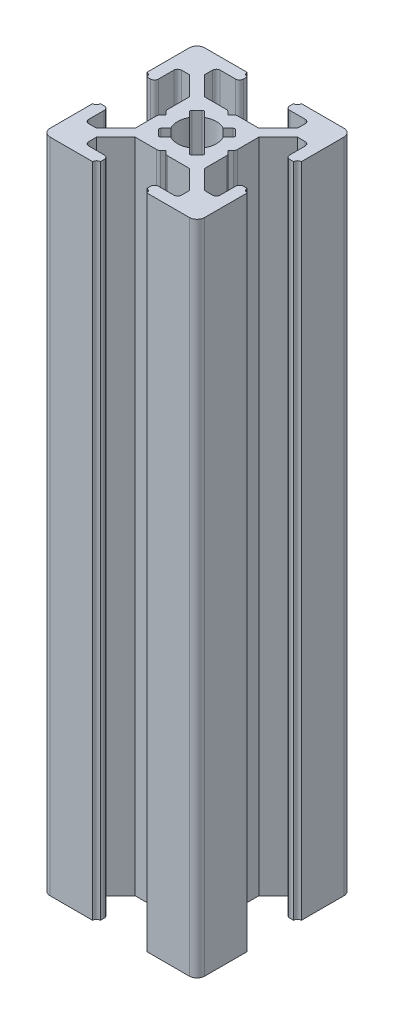
SolidWorks part; units mm, degrees
ref_plane "Front Plane" through (0, 0, 0) normal (0, 0, 1) x (1, 0, 0)
ref_plane "Top Plane" through (0, 0, 0) normal (0, 1, 0) x (1, 0, 0)
ref_plane "Right Plane" through (0, 0, 0) normal (1, 0, 0) x (0, 0, -1)
sketch "Sketch3" plane through (0, 0, 0) normal (0, 1, 0) x (1, 0, 0)
  line L0 (7, 20) -> (7, 18.5)
  line L1 (0, 0) -> (20, 0)
  line L2 (0, 0) -> (0, 20)
  line L3 (0, 20) -> (20, 20)
  line L4 (20, 0) -> (20, 20)
  line L5 (7, 18.5) -> (4, 18.5)
  line L6 (4, 18.5) -> (4, 17)
  line L7 (4, 17) -> (6.5, 14.5)
  line L8 (6.5, 14.5) -> (13.5, 14.5)
  line L9 (13.5, 14.5) -> (16, 17)
  line L10 (16, 17) -> (16, 18.5)
  line L11 (16, 18.5) -> (13, 18.5)
  line L12 (13, 18.5) -> (13, 20)
  line L13 (13, 20) -> (7, 20)
  line L14 (9.5, 14.5) -> (10, 14)
  line L15 (10, 14) -> (10.5, 14.5)
  line L16 (10.5, 14.5) -> (9.5, 14.5)
  line L17 (13, 19.5) -> (13, 20)
  line L18 (13.5, 20) -> (13, 20)
  line L19 (7, 19.5) -> (7, 20)
  line L20 (6.5, 20) -> (7, 20)
  line L21 (0, 13) -> (1.5, 13)
  line L22 (1.5, 13) -> (1.5, 16)
  line L23 (1.5, 16) -> (3, 16)
  line L24 (3, 16) -> (5.5, 13.5)
  line L25 (5.5, 13.5) -> (5.5, 6.5)
  line L26 (5.5, 6.5) -> (3, 4)
  line L27 (3, 4) -> (1.5, 4)
  line L28 (1.5, 4) -> (1.5, 7)
  line L29 (1.5, 7) -> (0, 7)
  line L30 (0, 7) -> (0, 13)
  line L31 (5.5, 10.5) -> (5.5, 9.5)
  line L32 (5.5, 9.5) -> (6, 10)
  line L33 (6, 10) -> (5.5, 10.5)
  line L34 (0.5, 13) -> (0, 13)
  line L35 (0, 13.5) -> (0, 13)
  line L36 (0, 6.5) -> (0, 7)
  line L37 (0.5, 7) -> (0, 7)
  line L38 (10, 20) -> (10, 0) construction
  line L39 (20, 10) -> (0, 10) construction
  line L40 (10, 6) -> (10.5, 5.5)
  line L41 (9.5, 5.5) -> (10, 6)
  line L42 (10.5, 5.5) -> (9.5, 5.5)
  line L43 (13.5, 0) -> (13, 0)
  line L44 (13, 0.5) -> (13, 0)
  line L45 (6.5, 0) -> (7, 0)
  line L46 (7, 0.5) -> (7, 0)
  line L47 (13, 1.5) -> (13, 0)
  line L48 (16, 1.5) -> (13, 1.5)
  line L49 (16, 3) -> (16, 1.5)
  line L50 (13.5, 5.5) -> (16, 3)
  line L51 (6.5, 5.5) -> (13.5, 5.5)
  line L52 (4, 3) -> (6.5, 5.5)
  line L53 (4, 1.5) -> (4, 3)
  line L54 (7, 1.5) -> (4, 1.5)
  line L55 (7, 0) -> (7, 1.5)
  line L56 (13, 0) -> (7, 0)
  line L57 (14.5, 9.5) -> (14, 10)
  line L58 (14.5, 10.5) -> (14.5, 9.5)
  line L59 (14, 10) -> (14.5, 10.5)
  line L60 (19.5, 7) -> (20, 7)
  line L61 (20, 6.5) -> (20, 7)
  line L62 (20, 13.5) -> (20, 13)
  line L63 (19.5, 13) -> (20, 13)
  line L64 (18.5, 7) -> (20, 7)
  line L65 (18.5, 4) -> (18.5, 7)
  line L66 (17, 4) -> (18.5, 4)
  line L67 (14.5, 6.5) -> (17, 4)
  line L68 (14.5, 13.5) -> (14.5, 6.5)
  line L69 (17, 16) -> (14.5, 13.5)
  line L70 (18.5, 16) -> (17, 16)
  line L71 (18.5, 13) -> (18.5, 16)
  line L72 (20, 13) -> (18.5, 13)
  line L73 (20, 7) -> (20, 13)
  arc A0 (13.5, 20) -> (13, 19.5) centre (13, 20) cw
  arc A1 (6.5, 20) -> (7, 19.5) centre (7, 20) ccw
  arc A2 (0.5, 13) -> (0, 13.5) centre (0, 13) ccw
  arc A3 (0.5, 7) -> (0, 6.5) centre (0, 7) cw
  arc A4 (13.5, 0) -> (13, 0.5) centre (13, 0) ccw
  arc A5 (6.5, 0) -> (7, 0.5) centre (7, 0) cw
  arc A6 (19.5, 7) -> (20, 6.5) centre (20, 7) ccw
  arc A7 (19.5, 13) -> (20, 13.5) centre (20, 13) cw
  point P7 (10, 14.5)
  point P16 (10, 20)
  point P26 (5.5, 10)
  point P35 (0, 10)
  dimension "D16" = 0.5
  dimension "D17" = 0.5
  dimension "D28" = 0.5
  dimension "D29" = 0.5
  dimension "D1" = 20
  dimension "D2" = 20
  dimension "D3" = 7
  dimension "D4" = 7
  dimension "D5" = 1.5
  dimension "D6" = 1.5
  dimension "D7" = 3
  dimension "D8" = 3
  dimension "D9" = 1.5
  dimension "D10" = 1.5
  dimension "D11" = 7
  dimension "D12" = 5.5
  dimension "D13" = 0.5
  dimension "D14" = 0.5
  dimension "D15" = 0.5
  dimension "D18" = 7
  dimension "D19" = 7
  dimension "D20" = 1.5
  dimension "D21" = 1.5
  dimension "D22" = 3
  dimension "D23" = 7
  dimension "D24" = 5.5
  dimension "D25" = 0.5
  dimension "D26" = 0.5
  dimension "D27" = 0.5
extrude "Boss-Extrude1" add sketch "Sketch3" along normal blind 85 contours L72 A7 L4 L3 A0 L12 L11 L10 L9 L8 L15 L14 L7 L6 L5 L0 A1 L2 A2 L21 L22 L23 L24 L25 L33 L32 L26 L27 L28 L29 A3 L1 A5 L55 L54 L53 L52 L51 L41 L40 L50 L49 L48 L47 A4
fillet "Fillet1" radius 1 4 edges at (0, 42.5, 0) (20, 42.5, 0) (20, 42.5, -20) (0, 42.5, -20)
sketch "Sketch4" plane through (0, 85, 0) normal (0, 1, 0) x (1, 0, 0)
  line L0 (13.5, 14.5) -> (5.5, 6.5) construction
  line L1 (14.5, 13.5) -> (6.5, 5.5) construction
  line L2 (10.5, 14.5) -> (14.5, 10.5) construction
  line L3 (12, 13) -> (13, 12)
  line L4 (13, 12) -> (8, 7)
  line L5 (8, 7) -> (7, 8)
  line L6 (7, 8) -> (12, 13)
  line L7 (13.5, 14.5) -> (16, 17) construction
  line L8 (17, 16) -> (14.5, 13.5) construction
  line L9 (5.5, 9.5) -> (9.5, 5.5) construction
  line L10 (5.5, 10.5) -> (9.5, 14.5) construction
  line L11 (14.5, 9.5) -> (10.5, 5.5) construction
  line L12 (6.5, 14.5) -> (14.5, 6.5) construction
  line L13 (5.5, 13.5) -> (13.5, 5.5) construction
  line L14 (7, 12) -> (8, 13)
  line L15 (8, 13) -> (13, 8)
  line L16 (13, 8) -> (12, 7)
  line L17 (12, 7) -> (7, 12)
  line L18 (4, 17) -> (6.5, 14.5) construction
  line L19 (3, 16) -> (5.5, 13.5) construction
  line L20 (20, 10) -> (0, 10) construction
  circle A0 centre (10, 10) radius 2.5
  dimension "D1" = 5
extrude "Cut-Extrude1" cut sketch "Sketch4" against normal through all contours L6 A0 L15 | L4 A0 L6 L15 | L15 A0 L17 L6 | L17 L4 L15 L6 | L17 A0 L6 | L6 A0 L4 L17 | L4 A0 L17 | L17 A0 L15 L4 | L15 A0 L4 | A0 L6 L5 L4 | A0 L17 L16 L15 | A0 L4 L3 L6 | A0 L15 L14 L17
fillet "Fillet2" radius 0.5 24 edges at (1.5, 42.5, -16) (1.5, 42.5, -13) (5.5, 42.5, -10.5) (5.5, 42.5, -9.5) (1.5, 42.5, -7) (1.5, 42.5, -4) (4, 42.5, -1.5) (7, 42.5, -1.5) (9.5, 42.5, -5.5) (10.5, 42.5, -5.5) (13, 42.5, -1.5) (16, 42.5, -1.5) (18.5, 42.5, -4) (18.5, 42.5, -7) (18.5, 42.5, -13) (18.5, 42.5, -16) (14.5, 42.5, -9.5) (14.5, 42.5, -10.5) (10.5, 42.5, -14.5) (9.5, 42.5, -14.5) (16, 42.5, -18.5) (13, 42.5, -18.5) (7, 42.5, -18.5) (4, 42.5, -18.5)
fillet "Fillet3" radius 0.25 8 edges at (13, 42.5, -8) (12, 42.5, -7) (13, 42.5, -12) (12, 42.5, -13) (8, 42.5, -13) (7, 42.5, -12) (7, 42.5, -8) (8, 42.5, -7)
